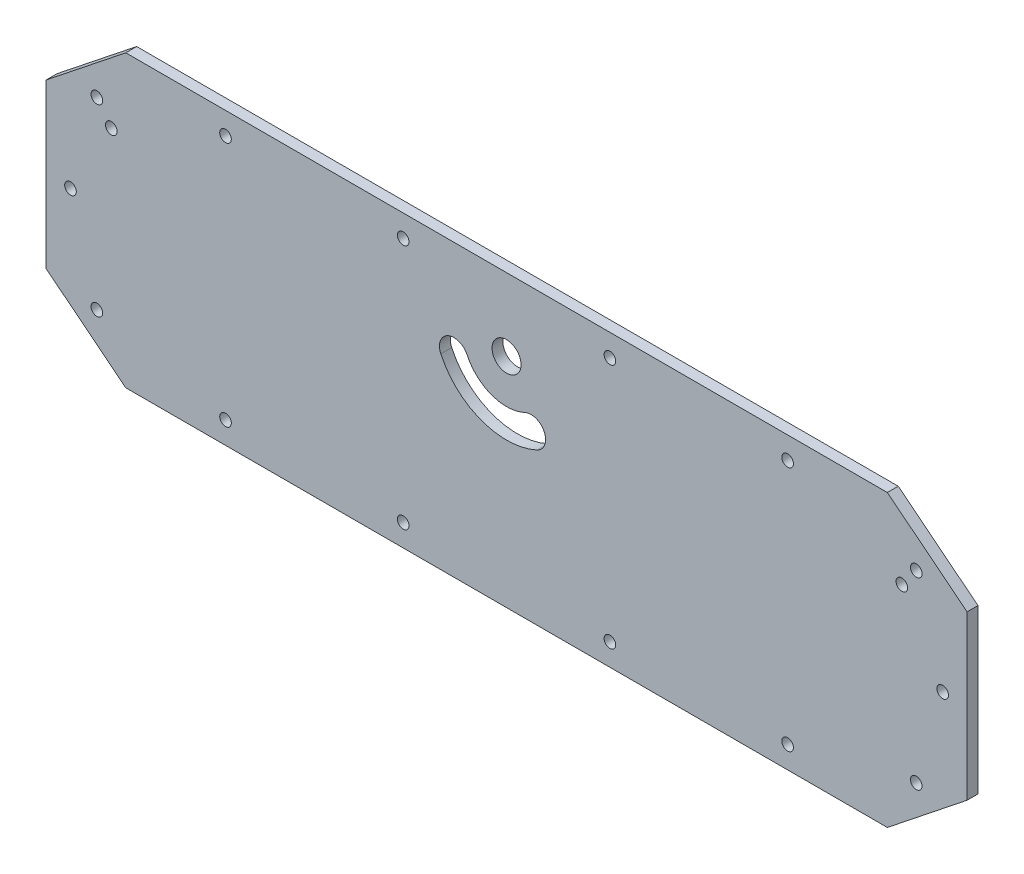
SolidWorks part; units mm, degrees
ref_plane "Alzado" through (0, 0, 0) normal (0, 0, 1) x (1, 0, 0)
ref_plane "Planta" through (0, 0, 0) normal (0, 1, 0) x (1, 0, 0)
ref_plane "Vista lateral" through (0, 0, 0) normal (1, 0, 0) x (0, 0, -1)
sketch "Croquis1" plane through (0, 0, 0) normal (0, 0, 1) x (1, 0, 0)
  line L0 (-127, 22.5) -> (-105, 40)
  line L1 (127, -40) -> (-127, -40) construction
  line L2 (127, -40) -> (127, 40) construction
  line L3 (127, 40) -> (-127, 40) construction
  line L4 (-127, -40) -> (-127, 40) construction
  line L5 (127, -40) -> (-127, 40) construction
  line L6 (127, 40) -> (-127, -40) construction
  line L7 (-105, 40) -> (105, 40)
  line L8 (105, 40) -> (127, 22.5)
  line L9 (127, 22.5) -> (127, -22.5)
  line L10 (127, -22.5) -> (105, -40)
  line L11 (105, -40) -> (-105, -40)
  line L12 (-105, -40) -> (-127, -22.5)
  line L13 (-127, -22.5) -> (-127, 22.5)
  line L14 (0, -40) -> (0, 40) construction
  line L15 (0, 33.9) -> (-28.5, 33.9) construction
  line L16 (-28.5, 33.9) -> (-77.5, 33.9) construction
  line L17 (0, 33.9) -> (28.5, 33.9) construction
  line L18 (28.5, 33.9) -> (77.5, 33.9) construction
  line L19 (0, -33.9) -> (-28.5, -33.9) construction
  line L20 (-28.5, -33.9) -> (-77.5, -33.9) construction
  line L21 (0, -33.9) -> (28.5, -33.9) construction
  line L22 (28.5, -33.9) -> (77.5, -33.9) construction
  line L23 (-127, 0) -> (-120.25, 0) construction
  line L24 (127, 0) -> (120.25, 0) construction
  line L25 (-18.1262, 11.5476) -> (-14.5009, 13.2381) construction
  line L26 (-112.98, -25.35) -> (112.98, -25.35) construction
  line L27 (-112.98, -25.35) -> (-112.98, 25.35) construction
  line L28 (-112.98, 25.35) -> (112.98, 25.35) construction
  line L29 (112.98, -25.35) -> (112.98, 25.35) construction
  line L30 (-112.98, -25.35) -> (112.98, 25.35) construction
  line L31 (-112.98, 25.35) -> (112.98, -25.35) construction
  line L32 (-14.5009, 13.2381) -> (-10.8757, 14.9286) construction
  line L33 (5.0714, 9.1243) -> (6.7619, 5.4991) construction
  line L34 (6.7619, 5.4991) -> (8.4524, 1.8738) construction
  line L35 (-5.4723, 4.9649) -> (0, 20) construction
  line L36 (0, 20) -> (-109, 20) construction
  line L37 (0, 20) -> (109, 20) construction
  circle A0 centre (0, 20) radius 4
  circle A1 centre (112.98, 25.35) radius 1.6
  circle A2 centre (120.25, 0) radius 1.6
  circle A3 centre (112.98, -25.35) radius 1.6
  circle A4 centre (77.5, -33.9) radius 1.6
  circle A5 centre (28.5, -33.9) radius 1.6
  circle A6 centre (-28.5, -33.9) radius 1.6
  circle A7 centre (-77.5, -33.9) radius 1.6
  circle A8 centre (-112.98, -25.35) radius 1.6
  circle A9 centre (-120.25, 0) radius 1.6
  circle A10 centre (-112.98, 25.35) radius 1.6
  circle A11 centre (-77.5, 33.9) radius 1.6
  circle A12 centre (-28.5, 33.9) radius 1.6
  circle A13 centre (28.5, 33.9) radius 1.6
  circle A14 centre (77.5, 33.9) radius 1.6
  arc A15 (-14.5009, 13.2381) -> (6.7619, 5.4991) centre (0, 20) ccw construction
  arc A16 (-18.1262, 11.5476) -> (8.4524, 1.8738) centre (0, 20) ccw
  arc A17 (-10.8757, 14.9286) -> (5.0714, 9.1243) centre (0, 20) ccw
  arc A18 (-10.8757, 14.9286) -> (-18.1262, 11.5476) centre (-14.5009, 13.2381) ccw
  arc A19 (8.4524, 1.8738) -> (5.0714, 9.1243) centre (6.7619, 5.4991) ccw
  circle A20 centre (-109, 20) radius 1.6
  circle A21 centre (109, 20) radius 1.6
  point P0 (0, 0)
  point P34 (0, 0)
  point P53 (-5.4723, 4.9649)
  dimension "D10" = 8
  dimension "D19" = 3.2
  dimension "D20" = 16
  dimension "D21" = 4
  dimension "D22" = 90
  dimension "D1" = 254
  dimension "D2" = 80
  dimension "D3" = 22
  dimension "D4" = 22
  dimension "D5" = 22
  dimension "D6" = 22
  dimension "D7" = 17.5
  dimension "D8" = 17.5
  dimension "D9" = 17.5
  dimension "D11" = 20
  dimension "D12" = 57
  dimension "D13" = 6.1
  dimension "D14" = 6.1
  dimension "D15" = 49
  dimension "D16" = 6.75
  dimension "D17" = 7.98
  dimension "D18" = 2.85
  dimension "D23" = 20
  dimension "D24" = 109
extrude "Saliente-Extruir1" add sketch "Croquis1" along normal blind 3
